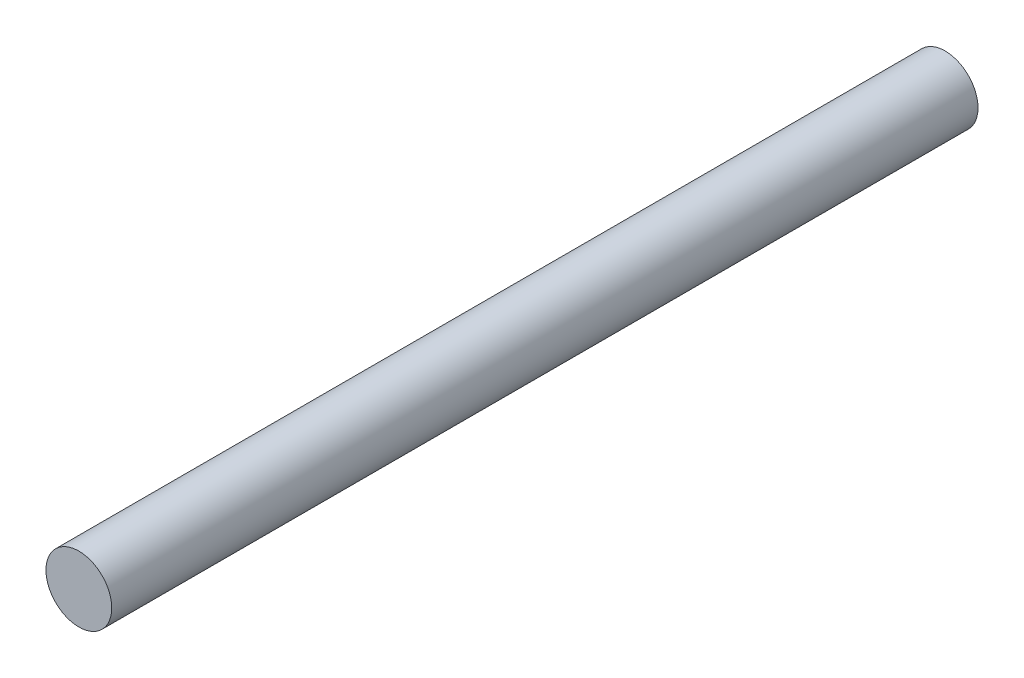
SolidWorks part; units mm, degrees
ref_plane "Plano frontal" through (0, 0, 0) normal (0, 0, 1) x (1, 0, 0)
ref_plane "Plano superior" through (0, 0, 0) normal (0, 1, 0) x (1, 0, 0)
ref_plane "Plano direito" through (0, 0, 0) normal (1, 0, 0) x (0, 0, -1)
sketch "Esboço1" plane through (0, 0, 0) normal (0, 0, 1) x (1, 0, 0)
  circle A0 centre (0, 0) radius 6
  dimension "D1" = 12
extrude "Ressalto-extrusão1" add sketch "Esboço1" along normal blind 158
